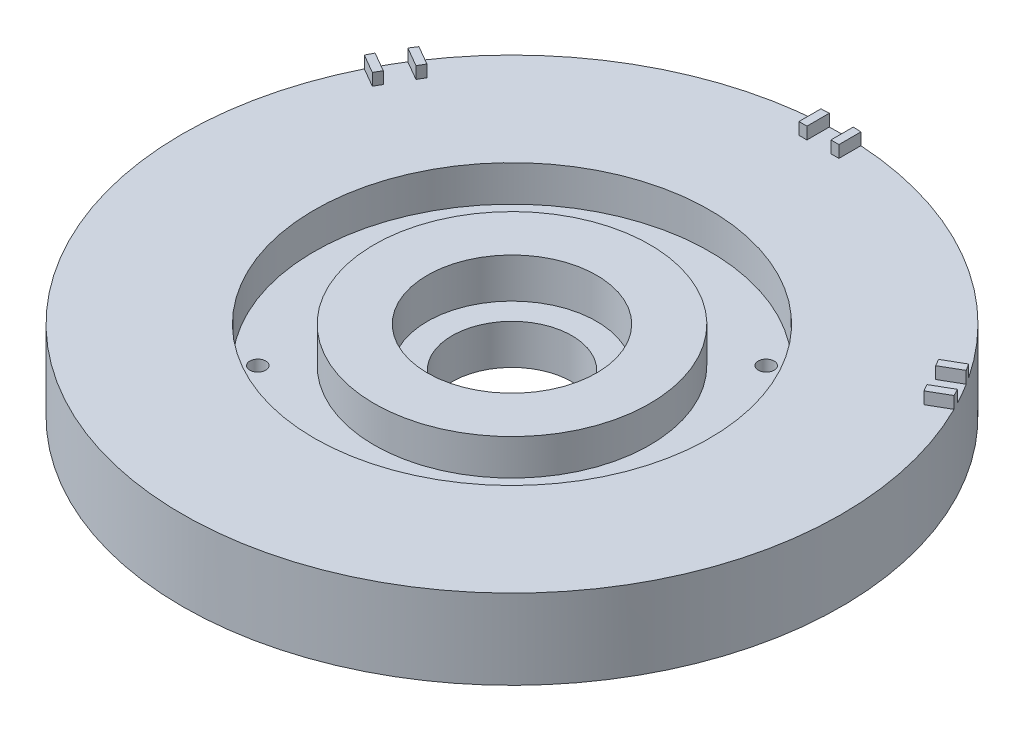
SolidWorks part; units mm, degrees
material "ABS"
ref_plane "Front Plane" through (0, 0, 0) normal (0, 0, 1) x (1, 0, 0)
ref_plane "Top Plane" through (0, 0, 0) normal (0, 1, 0) x (1, 0, 0)
ref_plane "Right Plane" through (0, 0, 0) normal (1, 0, 0) x (0, 0, -1)
sketch "Sketch1" plane through (0, 0, 0) normal (0, 1, 0) x (1, 0, 0)
  circle A0 centre (0, 0) radius 82.5
  dimension "D1" = 165
extrude "Boss-Extrude1" add sketch "Sketch1" along normal blind 20
sketch "Sketch2" plane through (0, 20, 0) normal (0, 1, 0) x (1, 0, 0)
  circle A0 centre (0, 0) radius 15
  dimension "D1" = 30
extrude "Cut-Extrude1" cut sketch "Sketch2" against normal blind 20
sketch "Sketch3" plane through (0, 20, 0) normal (0, 1, 0) x (1, 0, 0)
  circle A0 centre (0, 0) radius 49.5
  circle A1 centre (0, 0) radius 34.5
  dimension "D1" = 99
  dimension "D2" = 69
extrude "Cut-Extrude2" cut sketch "Sketch3" against normal blind 9
sketch "Sketch4" plane through (0, 0, 0) normal (0, -1, 0) x (1, 0, 0)
  circle A0 centre (0, 70) radius 2.5
  circle A1 centre (60.6218, 35) radius 2.5
  circle A2 centre (60.6218, -35) radius 2.5
  circle A3 centre (0, -70) radius 2.5
  circle A4 centre (-60.6218, -35) radius 2.5
  circle A5 centre (-60.6218, 35) radius 2.5
  point P12 (0, 0)
  point P16 (0, 0)
  dimension "D1" = 5
  dimension "D2" = 70
  dimension "D3" = 6
extrude "Cut-Extrude3" cut sketch "Sketch4" against normal blind 13
sketch "Sketch5" plane through (0, 0, 0) normal (0, -1, 0) x (1, 0, 0)
  line L0 (0, 0) -> (70.225, 70.225) construction
  line L1 (0, 0) -> (151.2534, 0) construction
  circle A0 centre (0, 0) radius 45 construction
  circle A1 centre (31.8198, 31.8198) radius 2
  circle A2 centre (31.8198, -31.8198) radius 2
  circle A3 centre (-31.8198, -31.8198) radius 2
  circle A4 centre (-31.8198, 31.8198) radius 2
  point P16 (0, 0)
  dimension "D1" = 90
  dimension "D3" = 4
  dimension "D2" = 45
  dimension "D4" = 4
extrude "Cut-Extrude4" cut sketch "Sketch5" against normal blind 17
sketch "Sketch7" plane through (0, 20, 0) normal (0, 1, 0) x (1, 0, 0)
  circle A0 centre (0, 0) radius 15 construction
  circle A1 centre (0, 0) radius 15
  circle A2 centre (0, 0) radius 21.2
  dimension "D1" = 42.4
extrude "Cut-Extrude5" cut sketch "Sketch7" against normal blind 10
sketch "Sketch8" plane through (0, 20, 0) normal (0, 1, 0) x (1, 0, 0)
  line L0 (0, 0) -> (0, 86.3852) construction
  line L1 (0, 0) -> (100.4595, 58.0003) construction
  line L2 (0, 0) -> (-85.1253, 49.1471) construction
  line L3 (-5, 82.3483) -> (-5, 76.8483)
  line L4 (-5, 76.8483) -> (-3, 76.8483)
  line L5 (5, 76.8483) -> (5, 82.3483)
  line L6 (64.0526, 42.7543) -> (65.0526, 41.0222)
  line L7 (64.0526, 42.7543) -> (68.8158, 45.5043)
  line L8 (69.0526, 34.094) -> (73.8158, 36.844)
  line L9 (-64.0526, 42.7543) -> (-68.8158, 45.5043)
  line L10 (-64.0526, 42.7543) -> (-65.0526, 41.0222)
  line L11 (-69.0526, 34.094) -> (-73.8158, 36.844)
  line L12 (-3, 76.8483) -> (-3, 82.4454)
  line L13 (3, 76.8483) -> (3, 82.4454)
  line L14 (65.0526, 41.0222) -> (69.8998, 43.8208)
  line L15 (68.0526, 35.8261) -> (72.8998, 38.6246)
  line L16 (-65.0526, 41.0222) -> (-69.8998, 43.8208)
  line L17 (-68.0526, 35.8261) -> (-72.8998, 38.6246)
  line L18 (3, 76.8483) -> (5, 76.8483)
  line L19 (68.0526, 35.8261) -> (69.0526, 34.094)
  line L20 (-68.0526, 35.8261) -> (-69.0526, 34.094)
  circle A0 centre (0, 0) radius 82.5 construction
  arc A1 (5, 82.3483) -> (3, 82.4454) centre (0, 0) ccw
  arc A2 (-68.8158, 45.5043) -> (-69.8998, 43.8208) centre (0, 0) ccw
  arc A3 (73.8158, 36.844) -> (72.8998, 38.6246) centre (0, 0) ccw
  arc A4 (-3, 82.4454) -> (-5, 82.3483) centre (0, 0) ccw
  arc A5 (69.8998, 43.8208) -> (68.8158, 45.5043) centre (0, 0) ccw
  arc A6 (-72.8998, 38.6246) -> (-73.8158, 36.844) centre (0, 0) ccw
  dimension "D1" = 60
  dimension "D2" = 60
  dimension "D3" = 5
  dimension "D4" = 5
  dimension "D5" = 5.5
  dimension "D6" = 5
  dimension "D7" = 5
  dimension "D8" = 5.5
  dimension "D9" = 2
  dimension "D10" = 2
  dimension "D11" = 2
  dimension "D12" = 2
extrude "Boss-Extrude2" add sketch "Sketch8" along normal blind 3
